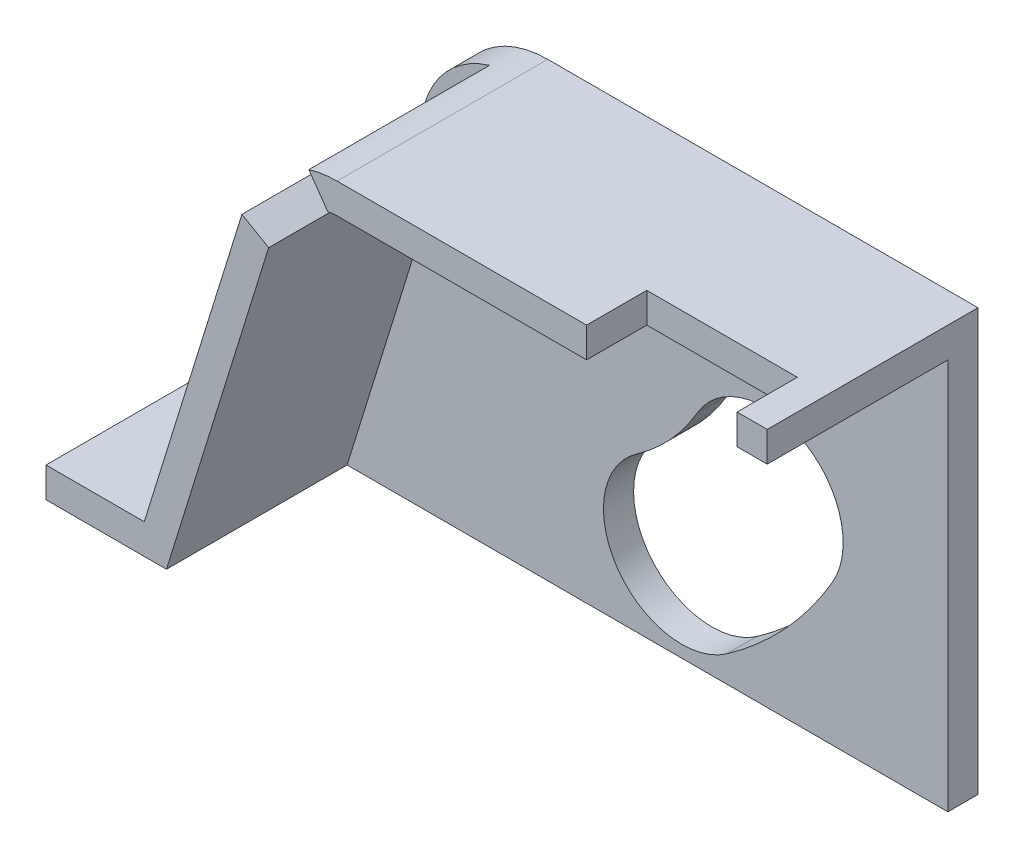
SolidWorks part; units mm, degrees
ref_plane "Front Plane" through (0, 0, 0) normal (0, 0, 1) x (1, 0, 0)
ref_plane "Top Plane" through (0, 0, 0) normal (0, 1, 0) x (1, 0, 0)
ref_plane "Right Plane" through (0, 0, 0) normal (1, 0, 0) x (0, 0, -1)
sketch "Sketch1" plane through (0, 0, 0) normal (0, 0, 1) x (1, 0, 0)
  line L1 (0, 0) -> (120, 0)
  line L2 (0, 0) -> (0, 100)
  line L3 (0, 100) -> (120, 100)
  line L4 (120, 0) -> (120, 100)
  dimension "D1" = 120
  dimension "D2" = 100
extrude "Boss-Extrude1" add sketch "Sketch1" along normal blind 5
sketch "Sketch2" plane through (0, 0, 5) normal (0, 0, 1) x (1, 0, 0)
  line L0 (0, 0) -> (120, 0) construction
  line L3 (83.2628, 4.351) -> (120, 30.0747) construction
  line L4 (120, 0) -> (120, 100) construction
  arc A0 (75.8063, 15) -> (89.605, 30) centre (48.5614, 53.9097) ccw construction
  arc A1 (83.2628, 4.351) -> (100.8379, 23.4563) centre (48.5614, 53.9097) ccw
  arc A2 (68.3498, 25.649) -> (78.372, 36.5437) centre (48.5614, 53.9097) ccw
  arc A3 (68.3498, 25.649) -> (83.2628, 4.351) centre (75.8063, 15) ccw
  arc A4 (100.8379, 23.4563) -> (78.372, 36.5437) centre (89.605, 30) ccw
  arc A5 (48.5614, 6.4097) -> (89.605, 30) centre (48.5614, 53.9097) ccw construction
  arc A6 (48.5614, -28.5903) -> (119.8476, 12.3823) centre (48.5614, 53.9097) ccw construction
  arc A7 (48.5614, 41.4097) -> (59.3623, 47.6177) centre (48.5614, 53.9097) ccw construction
  arc A8 (48.5614, 41.4097) -> (48.5614, -28.5903) centre (48.5614, 6.4097) ccw construction
  arc A9 (119.8476, 12.3823) -> (59.3623, 47.6177) centre (89.605, 30) ccw construction
  circle A10 centre (48.5614, 53.9097) radius 2.5
  point P3 (83.5196, 21.7512)
  point P17 (72.2314, 12.7274)
  point P27 (115, 5)
  dimension "D1" = 47.5
  dimension "D3" = 13
  dimension "D6" = 5
  dimension "D5" = 35
  dimension "D9" = 5
  dimension "D2" = 15
  dimension "D4" = 30
  dimension "D7" = 5
  dimension "D8" = 35
extrude "Cut-Extrude1" cut sketch "Sketch2" against normal through all
sketch "Sketch3" plane through (0, 0, 0) normal (0, 0, -1) x (-1, 0, 0)
  line L0 (0, 100) -> (0, 0) construction
  line L1 (-120, 0) -> (0, 0)
  line L2 (-120, 0) -> (-120, 1.6)
  line L3 (-120, 1.6) -> (0, 1.6)
  line L4 (0, 0) -> (0, 1.6)
  dimension "D1" = 1.6
extrude "Boss-Extrude2" [suppressed] add sketch "Sketch3" along normal blind 30
sketch "Sketch4" plane through (0, 0, 5) normal (0, 0, 1) x (1, 0, 0)
  line L0 (89.605, 30) -> (48.5614, 53.9097) construction
  line L1 (48.5614, 53.9097) -> (75.8063, 15) construction
  line L2 (92.6251, 35.1845) -> (51.5816, 59.0942) construction
  line L3 (52.6571, 56.7776) -> (79.902, 17.8679) construction
  line L4 (120, 0) -> (120, 100) construction
  line L5 (0, 0) -> (120, 0) construction
  arc A0 (65.8054, 38) -> (73, 46.617) centre (63.0497, 47.6128) ccw construction
  arc A1 (66.4943, 35.5968) -> (75.4876, 46.368) centre (63.0497, 47.6128) ccw
  arc A2 (65.1165, 40.4032) -> (70.5124, 46.8659) centre (63.0497, 47.6128) ccw
  arc A3 (65.1165, 40.4032) -> (66.4943, 35.5968) centre (65.8054, 38) ccw
  arc A4 (75.4876, 46.368) -> (70.5124, 46.8659) centre (73, 46.617) ccw
  point P13 (70.7259, 41.2037)
  dimension "D3" = 2.5
  dimension "D4" = 10
  dimension "D5" = 47
  dimension "D6" = 38
  dimension "D1" = 6
  dimension "D2" = 5
extrude "Cut-Extrude2" [suppressed] cut sketch "Sketch4" against normal through all
sketch "Sketch5" plane through (0, 0, 5) normal (0, 0, 1) x (1, 0, 0)
  line L0 (120, 70) -> (48.5614, 70)
  line L1 (120, 0) -> (120, 100) construction
  line L2 (33.1929, 58.6749) -> (15, 0)
  line L3 (0, 0) -> (120, 0) construction
  line L4 (15, 0) -> (0, 0)
  line L5 (0, 0) -> (0, 100)
  line L6 (0, 100) -> (120, 100)
  line L7 (120, 100) -> (120, 70)
  arc A0 (48.5614, 70) -> (33.1929, 58.6749) centre (48.5614, 53.9097) ccw
  circle A1 centre (48.5614, 53.9097) radius 2.5 construction
  dimension "D1" = 15
  dimension "D2" = 30
extrude "Cut-Extrude3" cut sketch "Sketch5" against normal blind 10
sketch "Sketch7" plane through (0, 0, 0) normal (0, 0, -1) x (-1, 0, 0)
  line L0 (-15, 0) -> (-32.773, 57.3206)
  line L1 (-120, 70) -> (-48.5614, 70)
  line L2 (-120, 70) -> (-120, 65)
  line L3 (-120, 65) -> (-48.5614, 65)
  line L5 (-33.1929, 58.6749) -> (-15, 0) construction
  line L7 (-37.207, 54.7377) -> (-20.2348, 0)
  line L8 (-15, 0) -> (-120, 0) construction
  line L9 (-20.2348, 0) -> (-15, 0)
  line L10 (-89.605, 30) -> (-48.5614, 53.9097) construction
  line L11 (-48.5614, 53.9097) -> (-29.5237, 65) construction
  line L12 (-75.8063, 15) -> (-48.5614, 53.9097) construction
  line L13 (-48.5614, 53.9097) -> (-34.8806, 73.4479) construction
  line L14 (-79.902, 17.8679) -> (-52.6571, 56.7776) construction
  line L15 (-52.6571, 56.7776) -> (-38.9763, 76.3158) construction
  line L16 (-87.0882, 25.6796) -> (-46.0446, 49.5893) construction
  line L17 (-46.0446, 49.5893) -> (-27.0069, 60.6796) construction
  line L18 (-47.0357, 64.8058) -> (-43.885, 69.3055)
  line L19 (-37.207, 54.7377) -> (-32.773, 57.3206)
  arc A0 (-48.5614, 70) -> (-43.885, 69.3055) centre (-48.5614, 53.9097) cw
  arc A1 (-33.1929, 58.6749) -> (-48.5614, 70) centre (-48.5614, 53.9097) ccw construction
  arc A2 (-48.5614, 65) -> (-47.0357, 64.8058) centre (-48.5614, 58.9097) cw
  dimension "D1" = 5
  dimension "D2" = 5
  dimension "D4" = 5
  dimension "D5" = 5
  dimension "D6" = 5
extrude "Boss-Extrude3" add sketch "Sketch7" along normal blind 30
sketch "Sketch8" plane through (0, 0, -30) normal (0, 0, -1) x (-1, 0, 0)
  line L0 (-20.2348, 0) -> (-15, 0) construction
  line L1 (-20.2348, 0) -> (-0.2348, 0)
  line L2 (-20.2348, 0) -> (-20.2348, 5)
  line L3 (-20.2348, 5) -> (-0.2348, 5)
  line L4 (-0.2348, 0) -> (-0.2348, 5)
  line L5 (-37.207, 54.7377) -> (-20.2348, 0) construction
  dimension "D1" = 20
  dimension "D2" = 5
extrude "Boss-Extrude4" add sketch "Sketch8" against normal through all
sketch "Sketch9" plane through (0, 70, 0) normal (0, 1, 0) x (1, 0, 0)
  line L1 (115, 30) -> (90, 30)
  line L2 (115, 30) -> (115, 20)
  line L3 (115, 20) -> (90, 20)
  line L4 (90, 30) -> (90, 20)
  line L5 (120, 30) -> (120, -5) construction
  line L6 (48.5614, 30) -> (120, 30) construction
  dimension "D1" = 10
  dimension "D3" = 25
  dimension "D4" = 5
extrude "Cut-Extrude4" cut sketch "Sketch9" against normal through all
mirror "Mirror1" about plane through (0, 0, 5) normal (0, 0, -1) of "Cut-Extrude4", "Boss-Extrude4", "Boss-Extrude3", "Cut-Extrude3", "Boss-Extrude1", "Cut-Extrude1"
sketch "Sketch10" plane through (120, 0, 0) normal (1, 0, 0) x (0, 0, -1)
  line L0 (-10, 0) -> (0, 0) construction
  line L1 (-5, 0) -> (30, 0)
  line L2 (-5, 0) -> (-5, 70)
  line L3 (-5, 70) -> (30, 70)
  line L4 (30, 0) -> (30, 70)
extrude "Cut-Extrude5" cut sketch "Sketch10" against normal through all
